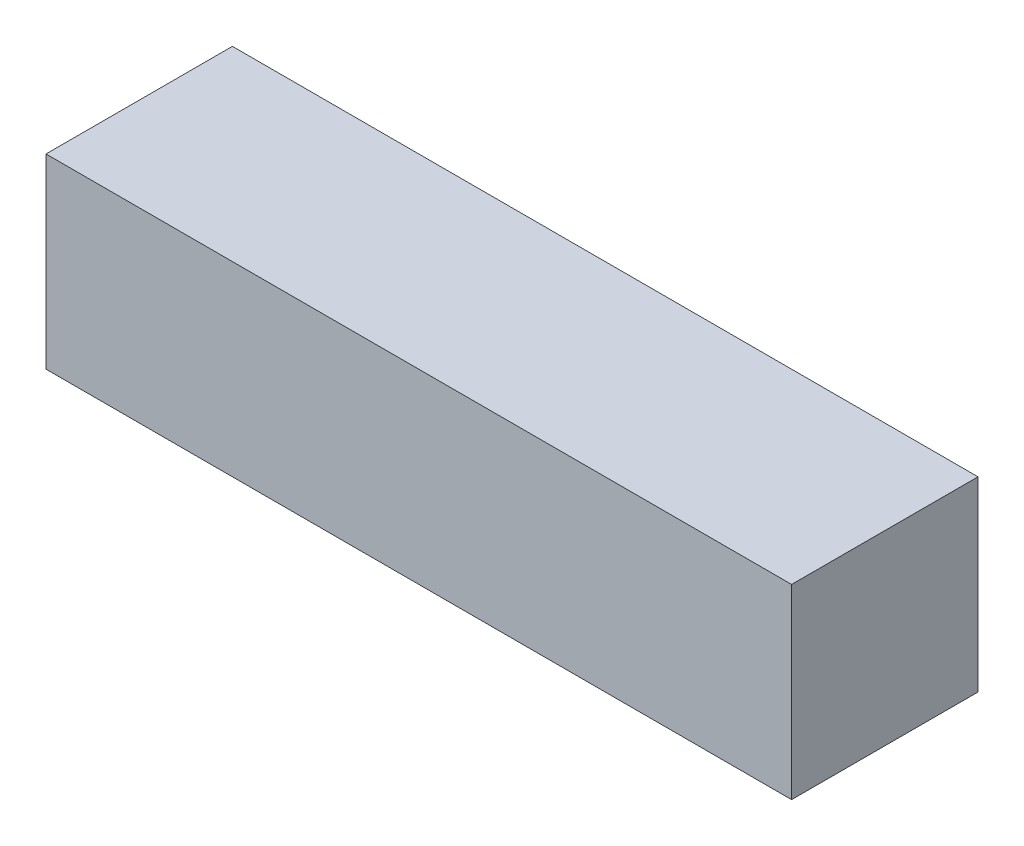
SolidWorks part; units mm, degrees
material "Balsa"
ref_plane "Front Plane" through (0, 0, 0) normal (0, 0, 1) x (1, 0, 0)
ref_plane "Top Plane" through (0, 0, 0) normal (0, 1, 0) x (1, 0, 0)
ref_plane "Right Plane" through (0, 0, 0) normal (1, 0, 0) x (0, 0, -1)
sketch "Sketch1" plane through (0, 0, 0) normal (1, 0, 0) x (0, 0, -1)
  line L0 (4.7625, -4.7625) -> (4.7625, 4.7625)
  line L1 (4.7625, 4.7625) -> (-4.7625, 4.7625)
  line L2 (-4.7625, 4.7625) -> (-4.7625, -4.7625)
  line L3 (-4.7625, -4.7625) -> (4.7625, -4.7625)
  point P2 (-5.1516, -2.0206)
  point P3 (0, 0)
  point P5 (-4.7625, 0)
  point P6 (0, 4.7625)
  dimension "D1" = 9.525
extrude "Boss-Extrude1" add sketch "Sketch1" along normal mid plane 38.1
